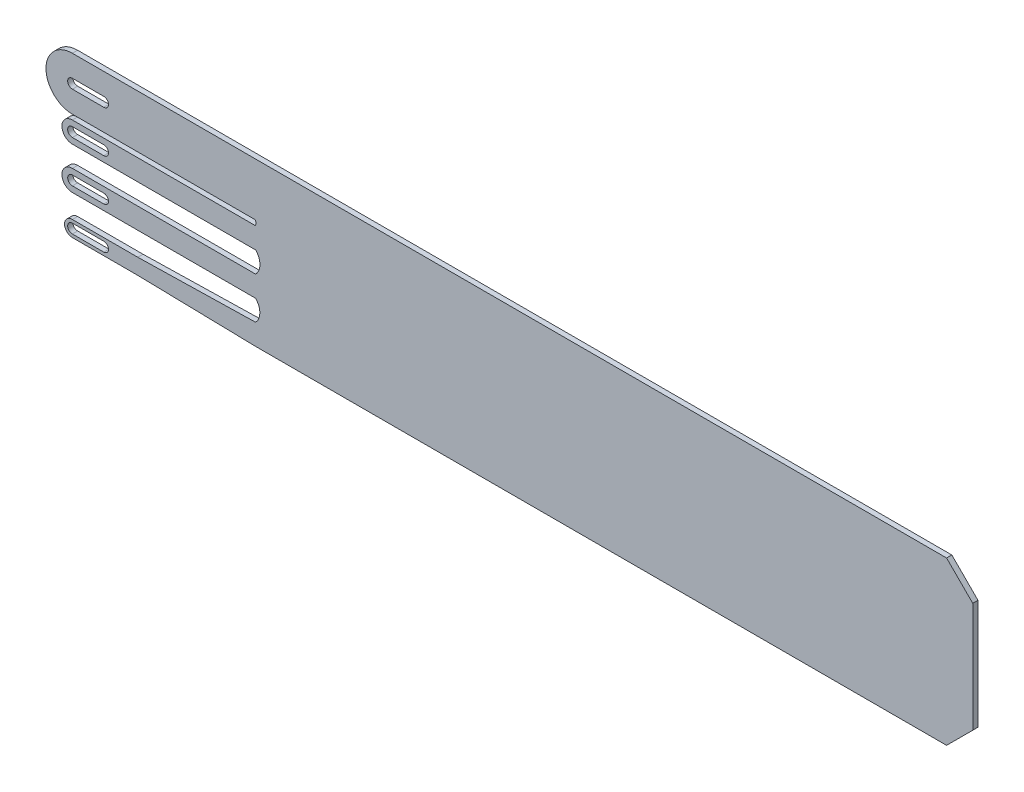
SolidWorks part; units mm, degrees
ref_plane "Front Plane" through (0, 0, 0) normal (0, 0, 1) x (1, 0, 0)
ref_plane "Top Plane" through (0, 0, 0) normal (0, 1, 0) x (1, 0, 0)
ref_plane "Right Plane" through (0, 0, 0) normal (1, 0, 0) x (0, 0, -1)
sketch "Esquisse4" plane through (0, 0, 0) normal (0, 0, 1) x (1, 0, 0)
  line L0 (-22.5, 3.5397) -> (-22.5, 0.5397)
  line L1 (0, 0.0397) -> (132, 0.0397)
  line L2 (132, 31.0397) -> (137, 26.0397)
  line L3 (0, 31.0397) -> (132, 31.0397)
  line L4 (137, 5.0397) -> (137, 26.0397)
  line L5 (0, 0.0397) -> (-22.5, 0.5397)
  line L6 (0, 8) -> (-35, 8)
  line L7 (0, 12) -> (-35, 12)
  line L8 (0, 20.9603) -> (-35, 20.9603)
  line L9 (0, 31.0397) -> (-35, 31.0397)
  line L10 (0, 16) -> (-35, 16)
  line L11 (132, 0.0397) -> (137, 5.0397)
  line L12 (0, 20) -> (-35, 20)
  line L13 (-35, 2.0397) -> (-29, 2.0397) construction
  line L14 (-35, 2.9397) -> (-29, 2.9397)
  line L15 (-35, 1.1397) -> (-29, 1.1397)
  line L16 (-35, 10) -> (-29, 10) construction
  line L17 (-35, 10.9) -> (-29, 10.9)
  line L18 (-35, 9.1) -> (-29, 9.1)
  line L19 (-35, 26) -> (-29, 26) construction
  line L20 (-35, 26.9) -> (-29, 26.9)
  line L21 (-35, 25.1) -> (-29, 25.1)
  line L22 (-35, 18) -> (-29, 18) construction
  line L23 (-35, 18.9) -> (-29, 18.9)
  line L24 (-35, 17.1) -> (-29, 17.1)
  line L25 (109.1533, 31.0397) -> (109.1533, 0.0397)
  line L26 (0, 4.0397) -> (-22.5, 3.5397)
  line L27 (-22.5, 0.5397) -> (-35, 0.5397)
  line L28 (-35, 3.5397) -> (-22.5, 3.5397)
  line L29 (-22.5, 8) -> (-22.5, 12)
  line L30 (0, 12) -> (-22.5, 12)
  arc A0 (-35, 0.5397) -> (-35, 3.5397) centre (-35, 2.0397) cw
  arc A1 (-35, 8) -> (-35, 12) centre (-35, 10) cw
  arc A2 (-35, 20.9603) -> (-35, 31.0397) centre (-35, 26) cw
  arc A3 (-35, 16) -> (-35, 20) centre (-35, 18) cw
  arc A4 (-35, 2.9397) -> (-35, 1.1397) centre (-35, 2.0397) ccw
  arc A5 (-29, 1.1397) -> (-29, 2.9397) centre (-29, 2.0397) ccw
  arc A6 (-35, 10.9) -> (-35, 9.1) centre (-35, 10) ccw
  arc A7 (-29, 9.1) -> (-29, 10.9) centre (-29, 10) ccw
  arc A8 (-35, 26.9) -> (-35, 25.1) centre (-35, 26) ccw
  arc A9 (-29, 25.1) -> (-29, 26.9) centre (-29, 26) ccw
  arc A10 (-35, 18.9) -> (-35, 17.1) centre (-35, 18) ccw
  arc A11 (-29, 17.1) -> (-29, 18.9) centre (-29, 18) ccw
  arc A12 (0, 20.9603) -> (0, 20) centre (-2.7874, 20.4802) cw
  arc A13 (0, 16) -> (0, 12) centre (-2, 14) cw
  arc A14 (0, 4.0397) -> (0, 8) centre (-2.0197, 6.0198) ccw
  point P1 (137, 28)
  point P3 (137, 0)
  point P8 (-32, 2.0397)
  point P32 (-32, 10)
  point P38 (-32, 26)
  point P44 (-32, 18)
extrude "Boss.-Extru.1" add sketch "Esquisse4" along normal blind 1 contours L3 L25 L1 L11 L4 L2 | A14 L26 L0 L5 L1 L25 L3 L9 A2 L8 A12 L12 A3 L10 A13 L7 L29 L6 A11 L24 A10 L23 A9 L21 A8 L20 | A1 L6 L29 L7 A7 L18 A6 L17 | A0 L27 L0 L28 A5 L15 A4 L14
